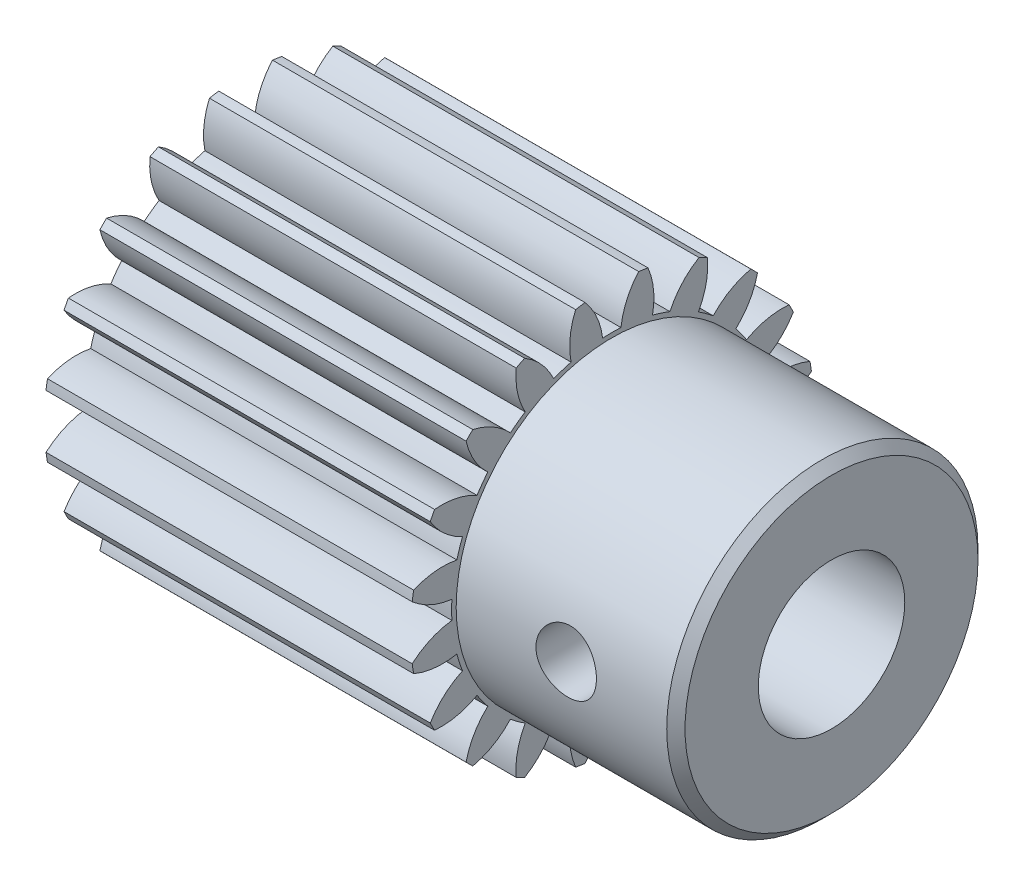
SolidWorks part; units mm, degrees
ref_plane "Plane1" through (0, 0, 0) normal (0, 0, 1) x (1, 0, 0)
ref_plane "Plane2" through (0, 0, 0) normal (0, 1, 0) x (1, 0, 0)
ref_plane "Plane3" through (0, 0, 0) normal (1, 0, 0) x (0, 0, -1)
sketch "HoldingSke" plane through (0, 0, 0) normal (0, 1, 0) x (1, 0, 0)
  line L0 (0, 0) -> (0.9397, -0.342)
  line L1 (-15, 0) -> (100, 0) construction
  line L2 (0, 0) -> (-2.1039, 2.3779)
  line L3 (0, 0) -> (-11.863, 4.5341)
  line L4 (0, 0) -> (8.1152, 2.9537)
  line L5 (0, 0) -> (-46.8476, -17.4728)
  line L6 (0, 0) -> (-8.2896, -5.593)
  line L7 (-2.1039, 2.3779) -> (8.6586, 51.2059)
  line L8 (-76.2, 54.61) -> (-74.8, 54.61)
  line L9 (-71.009, 38.7566) -> (-53.1078, 45.2721)
  line L10 (-76.2, 71.12) -> (104.1128, 71.12)
  line L11 (0, 0) -> (-10, 0)
  line L12 (-76.2, 101.6) -> (-76.162, 101.6)
  line L13 (24.9733, 27.94) -> (52.9518, 28.4284)
  line L14 (24.9733, 27.94) -> (24.9743, 27.94)
  line L15 (24.9733, 27.94) -> (100.4006, 29.5858)
  line L16 (-63.627, -1) -> (-12.827, -1)
  circle A0 centre (0, 0) radius 4
  circle A1 centre (0, 0) radius 8.749
  circle A2 centre (0, 0) radius 37.5
  circle A3 centre (0, 0) radius 4
  dimension "MHD" = 17.498
  dimension "Hub_dia" = 75
  dimension "Bore" = 8
  dimension "MBD" = 8
  dimension "Num_teeth" = 20
  dimension "Pitch" = 1
  dimension "Overall_len" = 50
  dimension "Show_teeth" = 20
  dimension "Thickness" = 10
  dimension "OAL" = 50.0001
  dimension "T_dim" = 1.4
  dimension "Ap" = 20
  dimension "H" = 19.05
  dimension "Pitch_radius" = 180.3128
  dimension "Width" = 10
  dimension "Backlash" = 0.038
  dimension "Addendum_fac" = 1
  dimension "Dedendum_fac" = 1.25
  dimension "Clearance_fac" = 0.25
  dimension "Dedendum_add" = 0.001
  dimension "Module" = 1
sketch "BasProSke" plane through (0, 0, 0) normal (0, 1, 0) x (1, 0, 0)
  line L0 (-10, 0) -> (60, 0) construction
  line L1 (0, 0) -> (0, 11)
  line L2 (0, 0) -> (20, 0)
  line L3 (20, 0) -> (20, 11)
  line L4 (20, 11) -> (0, 11)
  dimension "Thickness" = 20
  dimension "Diameter" = 22
revolve "Base-Revolve" add sketch "BasProSke" angle 360 about L0
sketch "TooCutSke" plane through (0, 0, 0) normal (1, 0, 0) x (0, 0, -1)
  line L1 (0, 0) -> (0, 107) construction
  line L2 (0, 0) -> (-0.8511, 9.9637) construction
  line L3 (0, 0) -> (-3.1206, 19.7028) construction
  line L4 (-0.8511, 9.9637) -> (-1.5603, 9.8514) construction
  arc A0 (0.4999, 8.7347) -> (-0.4999, 8.7347) centre (0, 0) ccw
  arc A1 (1.4852, 10.9249) -> (-1.4852, 10.9249) centre (0, 0) ccw
  circle A2 centre (0, 0) radius 10 construction
  circle A3 centre (0, 0) radius 9.3969 construction
  arc A4 (-0.4999, 8.7347) -> (-1.4852, 10.9249) centre (-4.4722, 8.2645) ccw
  arc A5 (1.4852, 10.9249) -> (0.4999, 8.7347) centre (4.4722, 8.2645) ccw
  dimension "Root_dia" = 17.498
  dimension "Overcut_dia" = 22.0508
  dimension "Pitch_dia" = 20
  dimension "Base_dia" = 18.7939
  dimension "Flank_rad" = 4
  dimension "Half_ang" = 9
  dimension "Half_CT" = 0.7181
extrude "ToothCut" cut sketch "TooCutSke" along normal through all
fillet "Breaks" [suppressed] radius 0.02
fillet "RootFillets" [suppressed] radius 0.251
pattern_circular "TeethCuts" count 20 every 18 about axis through (-10, 0, 0) along (1, 0, 0) of "ToothCut", "RootFillets", "Breaks"
sketch "HubNeaOneSke" plane through (0, 0, 0) normal (-1, 0, 0) x (0, 0, 1)
  circle A0 centre (0, 0) radius 8.749
  dimension "Diameter" = 17.498
extrude "HubNearOne" [suppressed] add sketch "HubNeaOneSke" along normal blind 30.0001
sketch "HubNeaBotSke" plane through (0, 0, 0) normal (-1, 0, 0) x (0, 0, 1)
  circle A0 centre (0, 0) radius 8.749
  dimension "Diameter" = 17.498
extrude "HubNearBoth" [suppressed] add sketch "HubNeaBotSke" along normal blind 15
ref_plane "FarPln" through (20, 0, 0) normal (1, 0, 0) x (0, 0, -1)
sketch "HubFarSke" plane through (20, 0, 0) normal (1, 0, 0) x (0, 0, -1)
  circle A0 centre (0, 0) radius 8.749
  dimension "Diameter" = 17.498
extrude "HubFar" [suppressed] add sketch "HubFarSke" along normal blind 15
sketch "草圖2" plane through (20, 0, 0) normal (1, 0, 0) x (0, 0, -1)
  circle A0 centre (0, 0) radius 8.5
  dimension "D1" = 17
extrude "填料-伸長1" add sketch "草圖2" along normal blind 12
sketch "BorSke" plane through (0, 0, 0) normal (1, 0, 0) x (0, 0, -1)
  circle A0 centre (0, 0) radius 4
  dimension "Diameter" = 8
extrude "Bore" cut sketch "BorSke" along normal mid plane 100.0001
sketch "KeySke" plane through (0, 0, 0) normal (1, 0, 0) x (0, 0, -1)
  line L0 (-1.5, 0) -> (-1.5, 5.4)
  line L1 (-1.5, 5.4) -> (1.5, 5.4)
  line L2 (1.5, 5.4) -> (1.5, 0)
  line L3 (0, 0) -> (0, 34) construction
  line L4 (-1.5, 0) -> (1.5, 0)
  dimension "Offset" = 5.4
  dimension "Width" = 3
extrude "Keyway" [suppressed] cut sketch "KeySke" along normal mid plane 100.0001
pattern_circular "Keyway2" [suppressed] count 2 every 90 about axis through (-10, 0, 0) along (1, 0, 0)
chamfer "導角1" distance 0.5 angle 45 1 edges at (32, 0, -8.5)
sketch "草圖3" plane through (0, 0, 0) normal (0, 1, 0) x (1, 0, 0)
  line L0 (26, -0.3561) -> (0, 0) construction
  line L1 (0, 0.4999) -> (0, -0.4999) construction
  line L2 (32, -8) -> (32, 8) construction
  circle A0 centre (26, -0.3561) radius 1.65
  dimension "D2" = 3.3
  dimension "D1" = 6
extrude "除料-伸長1" cut sketch "草圖3" against normal blind 10
pattern_circular "環狀複製排列1" count 2 over 90 about axis through (32, 0, 0) along (-1, 0, 0) of "除料-伸長1"
equation "' \"Module@HoldingSke\" = 6.35"
equation "' \"Num_teeth@HoldingSke\" = 12"
equation "' \"Ap@HoldingSke\" =  20"
equation "' \"Ap@HoldingSke\" = 20"
equation "' \"Width@HoldingSke\" = 0.5 * 25.4"
equation "' \"Hub_dia@HoldingSke\"= 1 * 25.4"
equation "' \"Hub_dia@HoldingSke\" = 1 * 25.4"
equation "' \"Overall_len@HoldingSke\" = 1.0 * 25.4"
equation "' \"Bore@HoldingSke\" = 0.75 * 25.4"
equation "' \"T_dim@HoldingSke\" = 0.1 * 25.4"
equation "' \"Width@KeySke\" = 0.25 * 25.4"
equation "' \"Show_teeth@HoldingSke\" = 13"
equation "' \"Backlash@HoldingSke\" = 0.009 * 25.4"
equation "' \"Addendum_fac@HoldingSke\" = 1.0"
equation "' \"Dedendum_fac@HoldingSke\" = 1.25"
equation "' \"Dedendum_add@HoldingSke\" = 0.00005 * 25.4"
equation "' \"Clearance_fac@HoldingSke\" = 0.25"
equation "\"Pitch@HoldingSke\" = 1 / \"Module@HoldingSke\""
equation "\"Overcut_dia@TooCutSke\" = (\"Num_teeth@HoldingSke\" + 2 * \"Addendum_fac@HoldingSke\") / \"Pitch@HoldingSke\" + 0.002 * 25.4"
equation "\"Pitch_dia@TooCutSke\" = \"Num_teeth@HoldingSke\" / \"Pitch@HoldingSke\""
equation "\"Base_dia@TooCutSke\" = \"Num_teeth@HoldingSke\" / \"Pitch@HoldingSke\" * cos((\"Ap@HoldingSke\"  * 3.14159265 / 180))"
equation "\"Root_dia@TooCutSke\" = (\"Num_teeth@HoldingSke\" + 2) / \"Pitch@HoldingSke\" - 2 * (\"Addendum_fac@HoldingSke\" + \"Dedendum_fac@HoldingSke\") / \"Pitch@HoldingSke\" - \"Dedendum_add@HoldingSke\" * 2"
equation "\"Half_ang@TooCutSke\" = 180 / \"Num_teeth@HoldingSke\""
equation "\"Half_CT@TooCutSke\" = \"Num_teeth@HoldingSke\" / \"Pitch@HoldingSke\" * sin((3.14159265 / 2 / \"Num_teeth@HoldingSke\")) / 2 - 7 * \"Backlash@HoldingSke\" / 4"
equation "\"Flank_rad@TooCutSke\" = \"Num_teeth@HoldingSke\" / \"Pitch@HoldingSke\" / 5"
equation "\"Radius@RootFillets\" = \"Clearance_fac@HoldingSke\" / \"Pitch@HoldingSke\" + \"Dedendum_add@HoldingSke\""
equation "\"Break_rad@Breaks\" = 0.02 / \"Pitch@HoldingSke\""
equation "\"Thickness@HoldingSke\" = \"Width@HoldingSke\""
equation "\"OAL@HoldingSke\" = \"Thickness@HoldingSke\""
equation "\"MHD@HoldingSke\" = (\"Num_teeth@HoldingSke\" + 2) / \"Pitch@HoldingSke\" - 2 * (\"Addendum_fac@HoldingSke\" + \"Dedendum_fac@HoldingSke\")  / \"Pitch@HoldingSke\" - \"Dedendum_add@HoldingSke\" * 2"
equation "\"MBD@HoldingSke\" = (\"Num_teeth@HoldingSke\" + 2) / \"Pitch@HoldingSke\" - 2 * (\"Addendum_fac@HoldingSke\" + \"Dedendum_fac@HoldingSke\")  / \"Pitch@HoldingSke\" - \"Dedendum_add@HoldingSke\" * 2 - 0.002 * 25.4"
equation "\"MHD@HoldingSke\" = ((sgn( \"MHD@HoldingSke\" - \"Hub_dia@HoldingSke\" )-1)*( \"MHD@HoldingSke\" - \"Hub_dia@HoldingSke\" ))/-2+ \"Hub_dia@HoldingSke\""
equation "\"MBD@HoldingSke\" = ((sgn( \"MBD@HoldingSke\" - \"Bore@HoldingSke\" )-1)*( \"MBD@HoldingSke\" - \"Bore@HoldingSke\" ))/-2+ \"Bore@HoldingSke\""
equation "\"OAL@HoldingSke\" = ((sgn( \"OAL@HoldingSke\" - \"Overall_len@HoldingSke\" )+1)*( \"OAL@HoldingSke\" - \"Overall_len@HoldingSke\" ))/2 + \"Overall_len@HoldingSke\" + 0.000002 * 25.4"
equation "\"Num_teeth@TeethCuts\" = int( \"Show_teeth@HoldingSke\" ) + 1"
equation "\"Num_teeth@TeethCuts\" = ((sgn( \"Num_teeth@TeethCuts\" - \"Num_teeth@HoldingSke\" )-1)*( \"Num_teeth@TeethCuts\" - \"Num_teeth@HoldingSke\" ))/-2+ \"Num_teeth@HoldingSke\""
equation "\"Num_teeth@TeethCuts\" = ((sgn( \"Num_teeth@TeethCuts\" - 2.0)+1)*( \"Num_teeth@TeethCuts\" - 2.0))/2 +2.0"
equation "\"Angle@TeethCuts\" = 360.0 / \"Num_teeth@HoldingSke\""
equation "\"Diameter@BasProSke\" = (\"Num_teeth@HoldingSke\" + 2 * \"Addendum_fac@HoldingSke\") / \"Pitch@HoldingSke\""
equation "' \"Fillet_rad@BasProSke\" =  \"Thickness@HoldingSke\" * 0.05"
equation "' \"Fillet_rad@BasProSke\" = \"Thickness@HoldingSke\" * 0.05"
equation "\"MHD@HoldingSke\" = ((sgn( \"MHD@HoldingSke\" - \"Root_dia@TooCutSke\" )-1)*( \"MHD@HoldingSke\" - \"Root_dia@TooCutSke\" ))/-2+ \"Root_dia@TooCutSke\""
equation "\"Diameter@HubNeaOneSke\" = \"MHD@HoldingSke\""
equation "\"Length@HubNearOne\" = \"OAL@HoldingSke\" - \"Thickness@BasProSke\""
equation "\"Diameter@HubNeaBotSke\" = \"MHD@HoldingSke\""
equation "\"Length@HubNearBoth\" = ( \"OAL@HoldingSke\" - \"Thickness@BasProSke\" ) / 2.0"
equation "\"Thickness@FarPln\" = \"Thickness@BasProSke\""
equation "\"Diameter@HubFarSke\" = \"MHD@HoldingSke\""
equation "\"Length@HubFar\" = ( \"OAL@HoldingSke\" - \"Thickness@BasProSke\" ) / 2.0"
equation "\"Diameter@BorSke\" = \"MBD@HoldingSke\""
equation "\"D1@Bore\" = \"OAL@HoldingSke\" * 2.0"
equation "\"D1@Keyway\" = \"OAL@HoldingSke\" * 2.0"
equation "\"Offset@KeySke\" = \"T_dim@HoldingSke\" + \"MBD@HoldingSke\" / 2.0"
